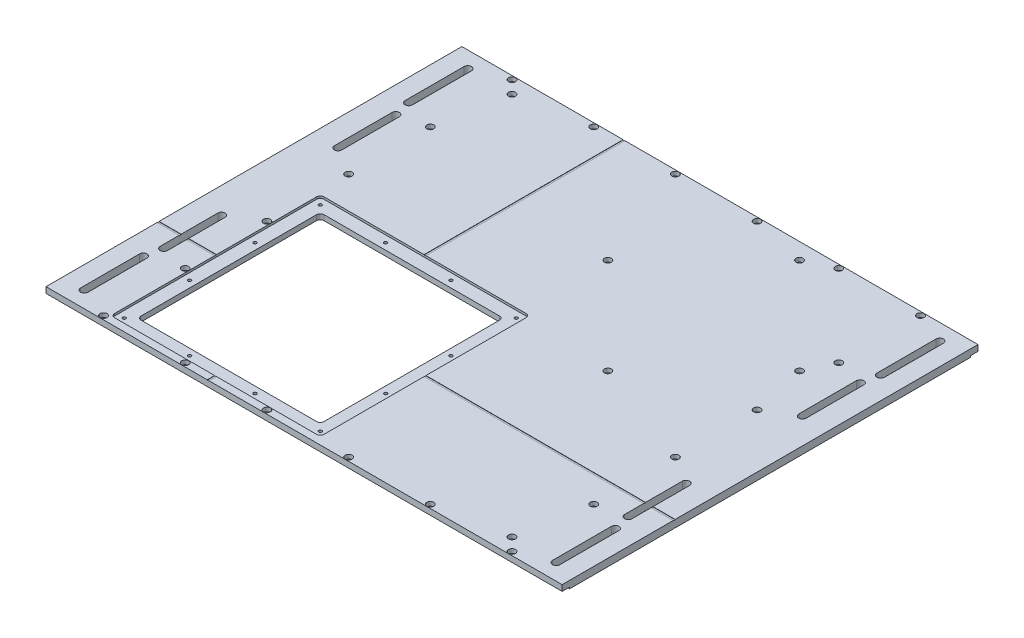
SolidWorks part; units mm, degrees
material "6061 Alloy"
ref_plane "Front Plane" through (0, 0, 0) normal (0, 0, 1) x (1, 0, 0)
ref_plane "Top Plane" through (0, 0, 0) normal (0, 1, 0) x (1, 0, 0)
ref_plane "Right Plane" through (0, 0, 0) normal (1, 0, 0) x (0, 0, -1)
sketch "Sketch1" plane through (0, 0, 0) normal (0, 1, 0) x (1, 0, 0)
  line L1 (0, 0) -> (444.5, 0)
  line L2 (0, 0) -> (0, 358.14)
  line L3 (0, 358.14) -> (444.5, 358.14)
  line L4 (444.5, 0) -> (444.5, 358.14)
  dimension "D1" = 444.5
  dimension "D2" = 358.14
extrude "Boss-Extrude1" add sketch "Sketch1" along normal blind 6.35
sketch "Sketch2" plane through (0, 6.35, 0) normal (0, 1, 0) x (1, 0, 0)
  line L1 (64.135, 17.78) -> (215.265, 17.78)
  line L2 (60.96, 20.955) -> (60.96, 172.085)
  line L3 (64.135, 175.26) -> (215.265, 175.26)
  line L4 (218.44, 20.955) -> (218.44, 172.085)
  line L6 (222.25, 358.14) -> (222.25, 0) construction
  line L7 (444.5, 358.14) -> (0, 358.14) construction
  line L8 (0, 0) -> (444.5, 0) construction
  line L9 (444.5, 179.07) -> (0, 179.07) construction
  line L10 (444.5, 0) -> (444.5, 358.14) construction
  line L11 (0, 358.14) -> (0, 0) construction
  arc A0 (215.265, 17.78) -> (218.44, 20.955) centre (215.265, 20.955) ccw
  arc A1 (64.135, 17.78) -> (60.96, 20.955) centre (64.135, 20.955) cw
  arc A2 (215.265, 175.26) -> (218.44, 172.085) centre (215.265, 172.085) cw
  arc A3 (60.96, 172.085) -> (64.135, 175.26) centre (64.135, 172.085) cw
  point P20 (60.96, 17.78)
  point P23 (218.44, 175.26)
  point P26 (60.96, 175.26)
  dimension "D3" = 3.175
  dimension "D1" = 157.48
  dimension "D2" = 157.48
  dimension "D4" = 7.62
  dimension "D5" = 7.62
extrude "Cut-Extrude1" cut sketch "Sketch2" against normal blind 6.35
sketch "Sketch3" plane through (0, 6.35, 0) normal (0, 1, 0) x (1, 0, 0)
  line L0 (64.135, 17.78) -> (215.265, 17.78) construction
  line L1 (52.705, 6.35) -> (226.695, 6.35)
  line L2 (49.53, 9.525) -> (49.53, 183.515)
  line L3 (52.705, 186.69) -> (226.695, 186.69)
  line L4 (229.87, 9.525) -> (229.87, 183.515)
  line L8 (218.44, 20.955) -> (218.44, 172.085) construction
  arc A0 (52.705, 186.69) -> (49.53, 183.515) centre (52.705, 183.515) ccw
  arc A1 (49.53, 9.525) -> (52.705, 6.35) centre (52.705, 9.525) ccw
  arc A2 (226.695, 6.35) -> (229.87, 9.525) centre (226.695, 9.525) ccw
  arc A3 (229.87, 183.515) -> (226.695, 186.69) centre (226.695, 183.515) ccw
  point P10 (49.53, 186.69)
  point P13 (49.53, 6.35)
  point P16 (229.87, 6.35)
  dimension "D5" = 3.175
  dimension "D1" = 180.34
  dimension "D2" = 180.34
  dimension "D3" = 11.43
  dimension "D4" = 11.43
extrude "Cut-Extrude2" cut sketch "Sketch3" against normal blind 1.8542
hole_wizard "CBORE for #6 Socket Head Cap Screw1" positions "Sketch10" profile "Sketch8" counterbore size "#6" standard "ANSI Inch" end condition through all
sketch "Sketch10" plane through (0, 6.35, 0) normal (0, 1, 0) x (1, 0, 0)
  line L0 (444.5, 358.14) -> (0, 358.14) construction
  line L2 (222.25, 358.14) -> (222.25, 304.2515) construction
  line L4 (353.1684, 309.9884) -> (222.25, 179.07) construction
  line L6 (444.5, 179.07) -> (263.845, 179.07) construction
  line L7 (444.5, 0) -> (444.5, 358.14) construction
  line L8 (0, 179.07) -> (444.5, 179.07) construction
  line L9 (0, 358.14) -> (0, 0) construction
  line L10 (222.25, 0) -> (222.25, 358.14) construction
  line L11 (0, 0) -> (444.5, 0) construction
  point P0 (46.355, 354.965)
  point P12 (116.713, 354.965)
  point P14 (187.071, 354.965)
  point P31 (398.145, 354.965)
  point P32 (327.787, 354.965)
  point P33 (257.429, 354.965)
  point P34 (398.145, 3.175)
  point P35 (327.787, 3.175)
  point P36 (257.429, 3.175)
  point P37 (187.071, 3.175)
  point P38 (116.713, 3.175)
  point P39 (46.355, 3.175)
  point P40 (398.145, 284.607)
  point P41 (398.145, 214.249)
  point P42 (398.145, 143.891)
  point P43 (398.145, 73.533)
  point P44 (46.355, 73.533)
  point P45 (46.355, 143.891)
  point P46 (46.355, 214.249)
  point P47 (46.355, 284.607)
  dimension "D1" = 3.175
  dimension "D2" = 70.358
  dimension "D3" = 35.179
  dimension "D4" = 70.358
  dimension "D5" = 45
sketch "Sketch8" plane through (46.355, 6.35, -354.965) normal (1, 0, 0) x (0, 0, 1)
  line L0 (0, 0) -> (0, 6.35)
  line L1 (0, 6.35) -> (1.8288, 6.35)
  line L3 (1.8288, 6.35) -> (1.8288, 3.5052)
  line L4 (1.8288, 3.5052) -> (3, 3.5052)
  line L5 (3, 3.5052) -> (3, 0)
  line L7 (3, 0) -> (0, 0)
  line L11 (0, -6.35) -> (0, 107.95) construction
  dimension "Thru Hole Dia." = 3.6576
  dimension "Thru Hole Depth" = 6.35
  dimension "C'Bore Dia." = 6
  dimension "C'Bore Depth" = 3.5052
hole_wizard "CBORE for #6 Socket Head Cap Screw2" positions "Sketch15" profile "Sketch16" counterbore size "#6" standard "ANSI Inch" end condition through all
sketch "Sketch15" plane through (249.4625, 6.35, -88.9524) normal (0, 1, 0) x (0, 0, 1)
  line L0 (88.9524, -27.2125) -> (-269.1876, -27.2125) construction
  line L1 (88.9524, -249.4625) -> (88.9524, 195.0375) construction
  line L2 (-269.1876, 195.0375) -> (-269.1876, -249.4625) construction
  line L3 (-269.1876, -27.2125) -> (-90.1176, 195.0375) construction
  line L4 (88.9524, 195.0375) -> (-269.1876, 195.0375) construction
  line L5 (-90.1176, 195.0375) -> (-90.1176, -249.4625) construction
  line L6 (-269.1876, -249.4625) -> (88.9524, -249.4625) construction
  line L7 (-90.1176, -249.4625) -> (88.9524, -27.2125) construction
  point P0 (-90.1176, 55.3375)
  point P3 (-172.6676, -27.2125)
  point P6 (-255.2176, -192.3125)
  point P9 (74.9824, 137.8875)
  point P12 (-172.6676, 137.8875)
  point P15 (-255.2176, 55.3375)
  dimension "D1" = 82.55
  dimension "D2" = 82.55
  dimension "D3" = 165.1
  dimension "D4" = 165.1
  dimension "D5" = 82.55
  dimension "D6" = 82.55
  dimension "D7" = 165.1
  dimension "D8" = 165.1
  dimension "D9" = 165.1
  dimension "D10" = 165.1
sketch "Sketch16" plane through (304.8, 6.35, -179.07) normal (1, 0, 0) x (0, 0, 1)
  line L0 (0, 0) -> (0, 6.35)
  line L1 (0, 6.35) -> (1.8288, 6.35)
  line L3 (1.8288, 6.35) -> (1.8288, 3.5052)
  line L4 (1.8288, 3.5052) -> (3, 3.5052)
  line L5 (3, 3.5052) -> (3, 0)
  line L7 (3, 0) -> (0, 0)
  line L11 (0, -6.35) -> (0, 107.95) construction
  dimension "Thru Hole Dia." = 3.6576
  dimension "Thru Hole Depth" = 6.35
  dimension "C'Bore Dia." = 6
  dimension "C'Bore Depth" = 3.5052
hole_wizard "Tap Drill for #6-32 Tap1" positions "Sketch17" profile "Sketch18" hole size "#6-32" standard "ANSI Inch"
sketch "Sketch17" plane through (249.4625, 4.4958, -88.9524) normal (0, 1, 0) x (0, 0, 1)
  line L0 (76.8155, -194.154) -> (76.8155, -25.371) construction
  line L1 (76.8155, -25.371) -> (-91.9506, -25.371) construction
  line L2 (-91.9506, -25.371) -> (-91.9506, -194.154) construction
  line L3 (-91.9506, -194.154) -> (76.8155, -194.154) construction
  line L9 (-7.5676, -31.0225) -> (-7.5676, -188.5025) construction
  line L10 (-83.1326, -31.0225) -> (67.9974, -31.0225) construction
  line L11 (67.9974, -188.5025) -> (-83.1326, -188.5025) construction
  line L12 (-7.5676, -188.5025) -> (71.1724, -109.7625) construction
  line L13 (71.1724, -34.1975) -> (71.1724, -185.3275) construction
  line L14 (71.1724, -109.7625) -> (-86.3076, -109.7625) construction
  line L15 (-86.3076, -185.3275) -> (-86.3076, -34.1975) construction
  point P0 (76.8155, -25.371)
  point P3 (20.5629, -25.371)
  point P6 (76.8155, -81.632)
  point P9 (76.8155, -137.893)
  point P12 (76.8155, -194.154)
  point P15 (20.5629, -194.154)
  point P18 (-35.6981, -194.154)
  point P21 (-91.9506, -194.154)
  point P24 (-91.9506, -137.893)
  point P27 (-91.9506, -81.632)
  point P30 (-91.9506, -25.371)
  point P33 (-35.6981, -25.371)
  dimension "D2" = 28.1305
  dimension "D3" = 28.1305
  dimension "D4" = 28.1305
  dimension "D5" = 56.2525
  dimension "D6" = 56.2525
  dimension "D7" = 56.2525
  dimension "D8" = 56.2525
  dimension "D9" = 56.261
  dimension "D10" = 56.261
  dimension "D11" = 56.261
  dimension "D12" = 56.261
  dimension "D13" = 28.1305
sketch "Sketch18" plane through (224.0915, 4.4958, -12.137) normal (1, 0, 0) x (0, 0, 1)
  line L0 (0, 0) -> (0, 5.3075)
  line L1 (0, 5.3075) -> (1.3525, 4.4948)
  line L2 (1.3525, 4.4948) -> (1.3525, 0)
  line L3 (1.3525, 0) -> (0, 0)
  line L4 (0, 5.3075) -> (-1.3526, 4.4948) construction
  line L5 (0, -6.35) -> (0, 107.95) construction
  dimension "Hole Dia." = 2.7051
  dimension "Hole Depth" = 4.4948
  dimension "Drill Angle" = 118
sketch "Sketch21" plane through (0, 0, 0) normal (0, -1, 0) x (1, 0, 0)
  line L1 (0, 0) -> (444.5, 0)
  line L2 (43.18, -6.35) -> (43.18, -351.79)
  line L3 (444.5, -358.14) -> (0, -358.14)
  line L4 (401.32, -6.35) -> (401.32, -351.79)
  line L6 (49.53, -6.35) -> (49.53, -351.79)
  line L7 (49.53, -351.79) -> (394.97, -351.79)
  line L8 (394.97, -6.35) -> (394.97, -351.79)
  line L9 (49.53, -6.35) -> (394.97, -6.35)
  line L10 (0, -358.14) -> (0, 0) construction
  line L11 (444.5, 0) -> (444.5, -358.14) construction
  line L12 (401.32, -351.79) -> (444.5, -351.79)
  line L13 (444.5, -351.79) -> (444.5, -358.14)
  line L14 (222.25, 0) -> (222.25, -358.14) construction
  line L15 (43.18, -351.79) -> (0, -351.79)
  line L16 (0, -351.79) -> (0, -358.14)
  line L18 (43.18, 0) -> (43.18, -358.14) construction
  line L19 (401.32, 0) -> (401.32, -358.14) construction
  line L20 (43.18, -6.35) -> (0, -6.35)
  line L21 (0, -6.35) -> (0, 0)
  line L23 (401.32, -6.35) -> (444.5, -6.35)
  line L24 (444.5, -6.35) -> (444.5, 0)
  line L30 (43.18, 0) -> (401.32, 0) construction
  line L31 (43.18, -358.14) -> (401.32, -358.14) construction
  dimension "D1" = 6.35
  dimension "D2" = 179.07
  dimension "D3" = 179.07
  dimension "D4" = 6.35
  dimension "D5" = 6.35
extrude "Cut-Extrude3" cut sketch "Sketch21" against normal blind 1.27
sketch "Sketch22" plane through (0, 0, 0) normal (0, -1, 0) x (1, 0, 0)
  line L0 (0, -179.07) -> (444.5, -179.07) construction
  line L1 (0, -351.79) -> (0, -6.35) construction
  line L2 (444.5, -6.35) -> (444.5, -351.79) construction
  line L3 (19.05, -17.8024) -> (19.05, -325.294) construction
  line L4 (444.5, 0) -> (0, 0) construction
  line L5 (222.25, 0) -> (222.25, -179.07) construction
  line L6 (222.25, -179.07) -> (222.25, -358.14) construction
  line L7 (0, -358.14) -> (444.5, -358.14) construction
  line L8 (422.25, -79.2415) -> (422.25, -128.8985) construction
  line L9 (19.05, -13.97) -> (19.05, -64.77) construction
  line L10 (425.425, -79.2415) -> (425.425, -128.8985)
  line L11 (22.2504, -13.97) -> (22.2504, -64.77)
  line L12 (15.8496, -13.97) -> (15.8496, -64.77)
  line L13 (19.05, -344.17) -> (19.05, -293.37) construction
  line L14 (419.075, -79.2415) -> (419.075, -128.8985)
  line L15 (422.25, -278.8985) -> (422.25, -229.2415) construction
  line L16 (22.2504, -344.17) -> (22.2504, -293.37)
  line L17 (15.8496, -344.17) -> (15.8496, -293.37)
  line L18 (425.45, -13.97) -> (425.45, -64.77) construction
  line L19 (422.2496, -13.97) -> (422.2496, -64.77)
  line L20 (428.6504, -13.97) -> (428.6504, -64.77)
  line L21 (425.45, -344.17) -> (425.45, -293.37) construction
  line L22 (422.2496, -344.17) -> (422.2496, -293.37)
  line L23 (428.6504, -344.17) -> (428.6504, -293.37)
  line L24 (425.425, -278.8985) -> (425.425, -229.2415)
  line L25 (419.075, -278.8985) -> (419.075, -229.2415)
  line L26 (22.25, -79.2415) -> (22.25, -128.8985) construction
  line L27 (422.25, -64.77) -> (422.25, -318.77) construction
  line L28 (19.075, -79.2415) -> (19.075, -128.8985)
  line L29 (25.425, -79.2415) -> (25.425, -128.8985)
  line L30 (22.25, -278.8985) -> (22.25, -229.2415) construction
  line L31 (19.075, -278.8985) -> (19.075, -229.2415)
  line L32 (25.425, -278.8985) -> (25.425, -229.2415)
  arc A0 (22.2504, -13.97) -> (15.8496, -13.97) centre (19.05, -13.97) ccw
  arc A1 (15.8496, -64.77) -> (22.2504, -64.77) centre (19.05, -64.77) ccw
  arc A2 (425.425, -79.2415) -> (419.075, -79.2415) centre (422.25, -79.2415) ccw
  arc A3 (419.075, -128.8985) -> (425.425, -128.8985) centre (422.25, -128.8985) ccw
  arc A4 (22.2504, -344.17) -> (15.8496, -344.17) centre (19.05, -344.17) cw
  arc A5 (15.8496, -293.37) -> (22.2504, -293.37) centre (19.05, -293.37) cw
  arc A6 (422.2496, -13.97) -> (428.6504, -13.97) centre (425.45, -13.97) cw
  arc A7 (428.6504, -64.77) -> (422.2496, -64.77) centre (425.45, -64.77) cw
  arc A8 (422.2496, -344.17) -> (428.6504, -344.17) centre (425.45, -344.17) ccw
  arc A9 (428.6504, -293.37) -> (422.2496, -293.37) centre (425.45, -293.37) ccw
  arc A10 (425.425, -278.8985) -> (419.075, -278.8985) centre (422.25, -278.8985) cw
  arc A11 (419.075, -229.2415) -> (425.425, -229.2415) centre (422.25, -229.2415) cw
  arc A12 (19.075, -79.2415) -> (25.425, -79.2415) centre (22.25, -79.2415) cw
  arc A13 (25.425, -128.8985) -> (19.075, -128.8985) centre (22.25, -128.8985) cw
  arc A14 (19.075, -278.8985) -> (25.425, -278.8985) centre (22.25, -278.8985) ccw
  arc A15 (25.425, -229.2415) -> (19.075, -229.2415) centre (22.25, -229.2415) ccw
  point P19 (422.25, -104.07)
  point P21 (19.05, -39.37)
  point P33 (19.05, -318.77)
  point P40 (425.45, -39.37)
  point P47 (425.45, -318.77)
  point P52 (422.25, -254.07)
  point P59 (22.25, -104.07)
  point P66 (22.25, -254.07)
  dimension "D3" = 49.657
  dimension "D7" = 75
  dimension "D1" = 203.2
  dimension "D2" = 200
  dimension "D4" = 50.8
  dimension "D5" = 139.7
  dimension "D6" = 6.35
extrude "Cut-Extrude4" cut sketch "Sketch22" against normal through all
sketch "Sketch24" plane through (0, 6.35, 0) normal (0, 1, 0) x (1, 0, 0)
  line L0 (139.7, 96.3284) -> (139.7, 0) construction
  line L1 (64.135, 175.26) -> (215.265, 175.26) construction
  line L2 (0, 0) -> (444.5, 0) construction
  line L3 (139.7, 0) -> (139.7, 358.14) construction
  line L4 (444.5, 358.14) -> (0, 358.14) construction
  line L5 (139.7, -7.62) -> (139.7, 358.14) construction
  line L6 (138.9062, -7.62) -> (138.9062, 95.7262)
  line L7 (140.4938, -7.62) -> (140.4937, 95.7262)
  line L8 (459.74, 96.52) -> (139.8915, 96.52) construction
  line L9 (229.87, 9.525) -> (229.87, 183.515) construction
  line L10 (459.74, 95.7263) -> (140.4937, 95.7262)
  line L11 (49.53, 96.52) -> (0, 96.52) construction
  line L12 (49.53, 183.515) -> (49.53, 9.525) construction
  line L13 (0, 358.14) -> (0, 0) construction
  line L14 (0, 96.52) -> (444.5, 96.52) construction
  line L15 (444.5, 0) -> (444.5, 358.14) construction
  line L16 (459.74, 97.3138) -> (140.4937, 97.3137)
  line L17 (138.9062, 97.3137) -> (0, 97.3137)
  line L18 (138.9062, 97.3137) -> (138.9062, 358.14)
  line L19 (140.4937, 97.3137) -> (140.4937, 358.14)
  line L20 (138.9062, 95.7262) -> (0, 95.7262)
  arc A0 (138.9062, -7.62) -> (140.4938, -7.62) centre (139.7, -7.62) ccw
  arc A1 (140.4937, 358.14) -> (138.9062, 358.14) centre (139.7, 358.14) ccw
  arc A2 (459.74, 95.7263) -> (459.74, 97.3138) centre (459.74, 96.52) ccw
  arc A3 (0, 97.3137) -> (0, 95.7262) centre (0, 96.52) ccw
  point P10 (139.7, 175.26)
  point P16 (229.87, 96.52)
  dimension "D1" = 1.5875
  dimension "D2" = 1.5875
extrude "Cut-Extrude6" cut sketch "Sketch24" against normal blind 0.254
sketch "Sketch25" plane through (0, 0, 0) normal (0, -1, 0) x (1, 0, 0)
  line L0 (60.96, -96.52) -> (0, -96.52) construction
  line L1 (60.96, -172.085) -> (60.96, -20.955) construction
  line L2 (218.44, -96.52) -> (444.5, -96.52) construction
  line L3 (218.44, -20.955) -> (218.44, -172.085) construction
  line L4 (0, -351.79) -> (0, -6.35) construction
  line L5 (444.5, -6.35) -> (444.5, -351.79) construction
  line L6 (-38.1, -96.52) -> (38.1, -96.52) construction
  line L7 (-38.1, -95.7263) -> (38.1, -95.7263)
  line L8 (-38.1, -97.3137) -> (38.1, -97.3137)
  line L9 (482.6, -96.52) -> (406.4, -96.52) construction
  line L10 (482.6, -97.3138) -> (406.4, -97.3138)
  line L11 (482.6, -95.7262) -> (406.4, -95.7262)
  arc A0 (-38.1, -95.7263) -> (-38.1, -97.3137) centre (-38.1, -96.52) ccw
  arc A1 (38.1, -97.3137) -> (38.1, -95.7263) centre (38.1, -96.52) ccw
  arc A2 (482.6, -97.3138) -> (482.6, -95.7262) centre (482.6, -96.52) ccw
  arc A3 (406.4, -95.7262) -> (406.4, -97.3138) centre (406.4, -96.52) ccw
  point P16 (0, -96.52)
  point P23 (444.5, -96.52)
extrude "Cut-Extrude7" cut sketch "Sketch25" against normal blind 0.254
